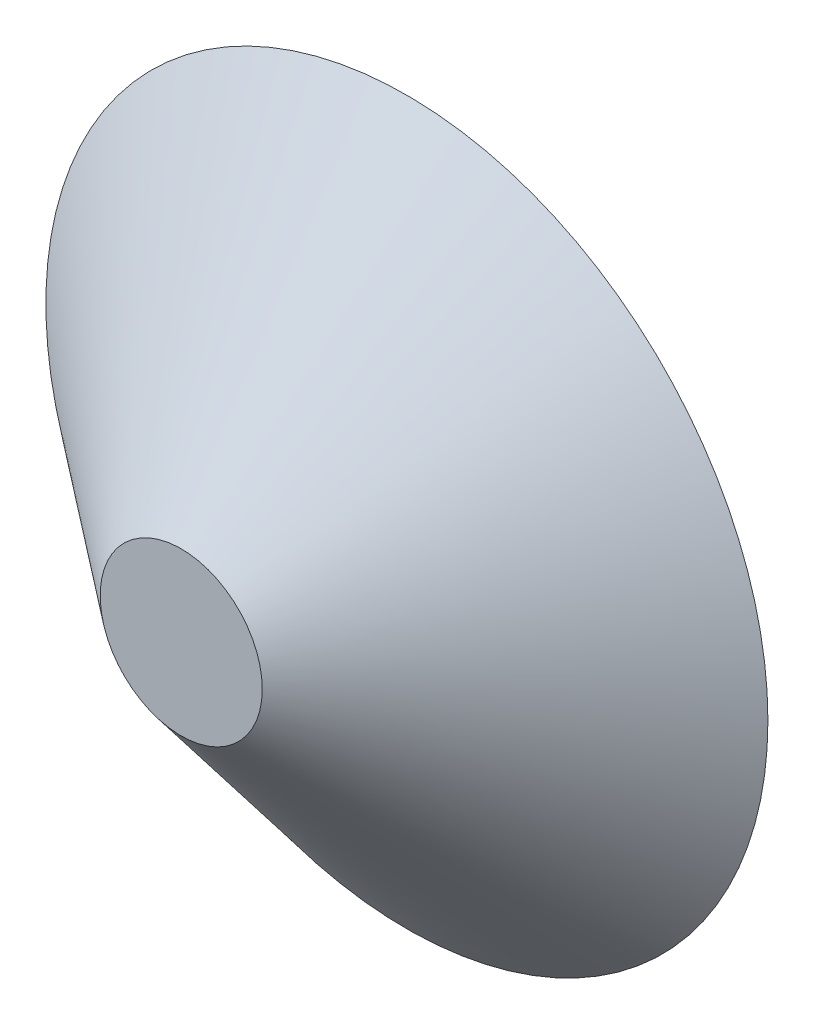
SolidWorks part; units mm, degrees
material "Tungsten"
ref_plane "Front" through (0, 0, 0) normal (0, 0, 1) x (1, 0, 0)
ref_plane "Top" through (0, 0, 0) normal (0, 1, 0) x (1, 0, 0)
ref_plane "Right" through (0, 0, 0) normal (1, 0, 0) x (0, 0, -1)
sketch "Sketch1" plane through (0, 0, 0) normal (0, 0, 1) x (1, 0, 0)
  circle A0 centre (0, 0) radius 71.67
extrude "Boss-Extrude4" add sketch "Sketch1" along normal blind 44.8 draft 51.13
